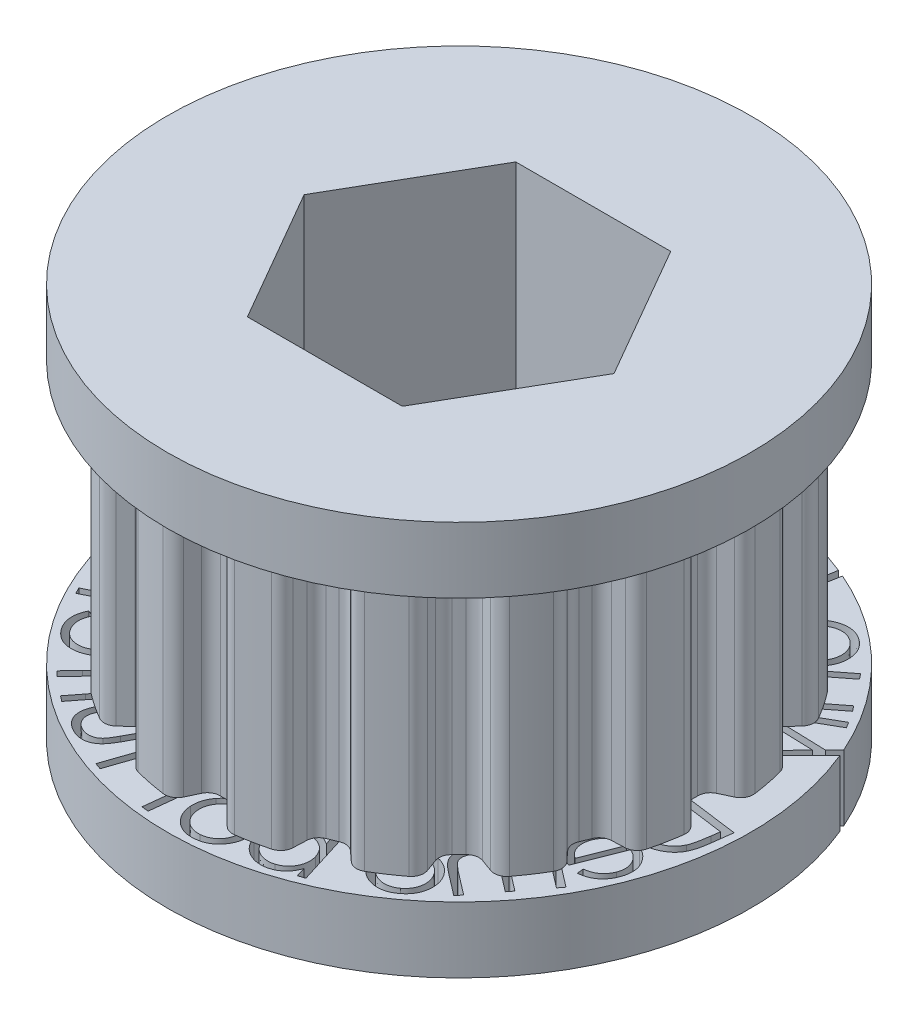
SolidWorks part; units mm, degrees
material "ABS"
ref_plane "Front Plane" through (0, 0, 0) normal (0, 0, 1) x (1, 0, 0)
ref_plane "Top Plane" through (0, 0, 0) normal (0, 1, 0) x (1, 0, 0)
ref_plane "Right Plane" through (0, 0, 0) normal (1, 0, 0) x (0, 0, -1)
sketch "Sketch1" plane through (0, 0, 0) normal (0, 1, 0) x (1, 0, 0)
  line L0 (0, 0) -> (0, 12.9361) construction
  circle A0 centre (0, 0) radius 12.9361
  point P6 (0, 210.65)
extrude "Boss-Extrude1" add sketch "Sketch1" along normal blind 12.7
sketch "Sketch2" plane through (0, 12.7, 0) normal (0, 1, 0) x (1, 0, 0)
  line L0 (0, 0) -> (0, 12.9361) construction
  line L2 (-0.8063, 11.6316) -> (-1.0802, 12.2189)
  line L3 (0.8063, 11.6316) -> (1.0802, 12.2189)
  line L4 (0, 0) -> (2.4742, 12.4384) construction
  line L5 (-2.4742, 12.4384) -> (0, 0) construction
  line L6 (-2.4742, 12.4384) -> (-2.5237, 12.6875)
  line L7 (2.4742, 12.4384) -> (2.5237, 12.6875)
  circle A0 centre (0, 0) radius 12.9361 construction
  arc A1 (1.7156, 12.5655) -> (2.4742, 12.4384) centre (0, 0) cw
  arc A2 (-1.7156, 12.5655) -> (-2.4742, 12.4384) centre (0, 0) ccw
  arc A3 (2.5237, 12.6875) -> (-2.5237, 12.6875) centre (0, 0) ccw
  arc A4 (-0.2405, 11.2796) -> (0.2405, 11.2796) centre (0, 0) cw
  arc A5 (1.0802, 12.2189) -> (1.7156, 12.5655) centre (1.633, 11.9612) cw
  arc A6 (0.2405, 11.2796) -> (0.8063, 11.6316) centre (0.2535, 11.8894) ccw
  arc A7 (-0.2405, 11.2796) -> (-0.8063, 11.6316) centre (-0.2535, 11.8894) cw
  arc A8 (-1.0802, 12.2189) -> (-1.7156, 12.5655) centre (-1.633, 11.9612) ccw
  point P7 (0, 212.2279)
  point P16 (0, 11.2821)
  point P19 (0.635, 11.2642)
  point P22 (-0.635, 11.2642)
extrude "Cut-Extrude1" cut sketch "Sketch2" against normal through all
pattern_circular "CirPattern1" count 16 over 360 about axis through (0, 0, 0) along (0, 1, 0) of "Cut-Extrude1"
sketch "Sketch3" plane through (0, 12.7, 0) normal (0, 1, 0) x (1, 0, 0)
  circle A0 centre (0, 0) radius 14.0821
  arc A1 (3.2237, 12.2656) -> (1.7156, 12.5655) centre (0, 0) ccw construction
extrude "Boss-Extrude2" add sketch "Sketch3" along normal blind 3.175
sketch "Sketch4" plane through (0, 0, 0) normal (0, -1, 0) x (1, 0, 0)
  circle A0 centre (0, 0) radius 14.0821 construction
  circle A1 centre (0, 0) radius 14.0821
extrude "Boss-Extrude3" add sketch "Sketch4" along normal blind 3.175
sketch "Sketch5" plane through (0, -3.175, 0) normal (0, -1, 0) x (1, 0, 0)
  line L1 (-3.7395, -6.477) -> (3.7395, -6.477)
  line L2 (3.7395, -6.477) -> (7.479, 0)
  line L3 (7.479, 0) -> (3.7395, 6.477)
  line L4 (3.7395, 6.477) -> (-3.7395, 6.477)
  line L5 (-3.7395, 6.477) -> (-7.479, 0)
  line L6 (-7.479, 0) -> (-3.7395, -6.477)
  circle A0 centre (0, 0) radius 6.477 construction
  dimension "D1" = 12.954
extrude "Cut-Extrude2" cut sketch "Sketch5" against normal through all
sketch "Sketch6" plane through (0, -3.175, 0) normal (0, -1, 0) x (1, 0, 0)
  circle A0 centre (0, 0) radius 13.7541 construction
  text T0 "Demo bot turret turn (not spin) only\r\n"
extrude "Cut-Extrude3" cut sketch "Sketch6" against normal blind 3.175
equation "\"Pitch\"= 0.2in"
equation "\"Number of Teeth\"= 16"
equation "\"Flank Angle\"= 50deg"
equation "\"Tooth bottom width\"= 1.27mm"
equation "\"Tooth height\"= 1.4mm"
equation "\"Fillet Radius\"= 0.61mm"
equation "\"Pitch zone\"= 0.254mm"
equation "\"D1@Sketch1\"=\"Pitch\" * \"Number of Teeth\" / pi"
equation "\"Width\"= 0.5in"
equation "\"D1@Boss-Extrude1\"=\"Width\""
equation "\"D1@Sketch2\"=\"Tooth bottom width\""
equation "\"D2@Sketch2\"=\"Flank Angle\""
equation "\"D3@Sketch2\"=\"Flank Angle\"/2"
equation "\"D4@Sketch2\"=180 / \"Number of Teeth\""
equation "\"D5@Sketch2\"= 180 / \"Number of Teeth\""
equation "\"D6@Sketch2\"=\"Pitch zone\""
equation "\"D7@Sketch2\"=\"Tooth height\""
equation "\"D1@CirPattern1\"=\"Number of Teeth\""
equation "\"D1@Sketch3\"=\"Tooth height\""
